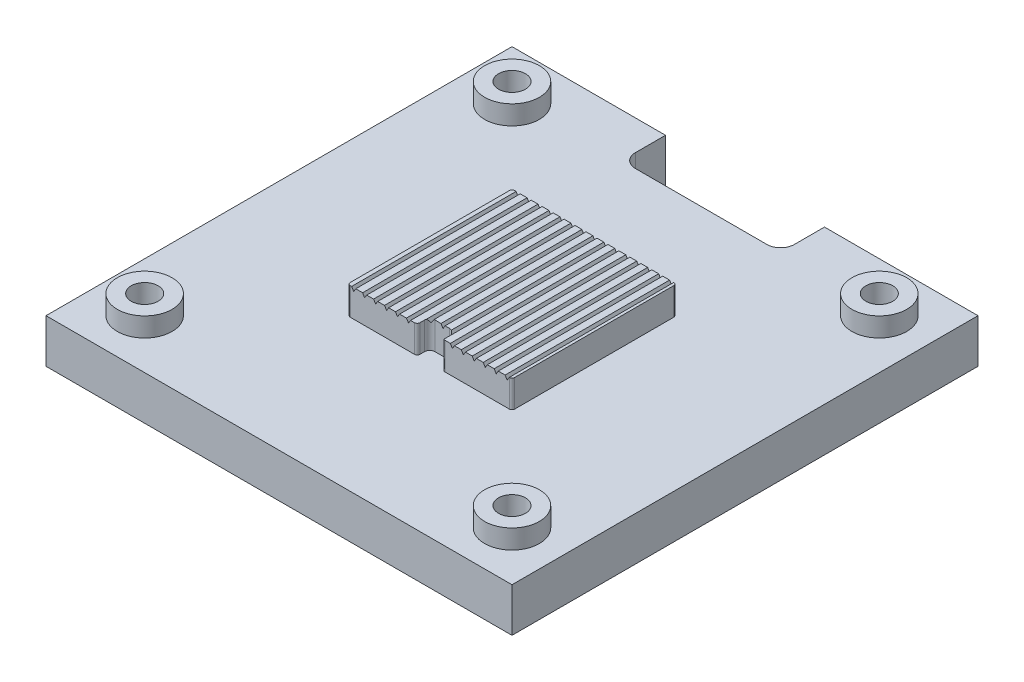
SolidWorks part; units mm, degrees
ref_plane "Front Plane" through (0, 0, 0) normal (0, 0, 1) x (1, 0, 0)
ref_plane "Top Plane" through (0, 0, 0) normal (0, 1, 0) x (1, 0, 0)
ref_plane "Right Plane" through (0, 0, 0) normal (1, 0, 0) x (0, 0, -1)
sketch "Sketch1" plane through (0, 0, 0) normal (0, 1, 0) x (1, 0, 0)
  line L0 (-71.3469, 0) -> (71.3469, 0) construction
  line L1 (-42.5, 42.5) -> (42.5, 42.5)
  line L2 (-42.5, 42.5) -> (-42.5, -42.5)
  line L3 (-42.5, -42.5) -> (42.5, -42.5)
  line L4 (42.5, 42.5) -> (42.5, -42.5)
  line L5 (-42.5, 42.5) -> (42.5, -42.5) construction
  line L6 (-42.5, -42.5) -> (42.5, 42.5) construction
  line L7 (0, -59.0713) -> (0, 59.0713) construction
  circle A0 centre (-33.5, 33.5) radius 2.4575
  circle A1 centre (-33.5, -33.5) radius 2.4575
  circle A2 centre (33.5, -33.5) radius 2.4575
  circle A3 centre (33.5, 33.5) radius 2.4575
  point P0 (0, 0)
  dimension "D3" = 4.915
  dimension "D1" = 85
  dimension "D2" = 85
  dimension "D4" = 9
  dimension "D5" = 9
extrude "Boss-Extrude1" add sketch "Sketch1" along normal blind 8
sketch "Sketch2" plane through (0, 0, 0) normal (0, -1, 0) x (1, 0, 0)
  line L0 (0, -4.4) -> (0, 4.4) construction
  line L1 (4.4, 0) -> (-4.4, 0) construction
  circle A0 centre (-33.5, 33.5) radius 3.969
  circle A1 centre (33.5, 33.5) radius 3.969
  circle A2 centre (33.5, -33.5) radius 3.969
  circle A3 centre (-33.5, -33.5) radius 3.969
  dimension "D1" = 7.938
extrude "Cut-Extrude1" cut sketch "Sketch2" against normal blind 4.166
sketch "Sketch3" plane through (0, 8, 0) normal (0, 1, 0) x (1, 0, 0)
  line L0 (0, -4.4) -> (0, 4.4) construction
  line L1 (-4.4, 0) -> (4.4, 0) construction
  circle A0 centre (33.5, -33.5) radius 5
  circle A1 centre (33.5, -33.5) radius 2.4575
  circle A2 centre (33.5, -33.5) radius 2.4575 construction
  circle A3 centre (-33.5, -33.5) radius 2.4575
  circle A4 centre (-33.5, -33.5) radius 5
  circle A5 centre (-33.5, 33.5) radius 5
  circle A6 centre (-33.5, 33.5) radius 2.4575
  circle A7 centre (33.5, 33.5) radius 2.4575
  circle A8 centre (33.5, 33.5) radius 5
  dimension "D1" = 10
extrude "Boss-Extrude2" add sketch "Sketch3" along normal blind 3.5
sketch "Sketch4" plane through (0, 8, 0) normal (0, 1, 0) x (1, 0, 0)
  line L0 (2.2929, -14.5) -> (2.2929, -13.7071)
  line L1 (14.5, -15) -> (2.7929, -15)
  line L2 (15, -14.5) -> (15, 14.5)
  line L3 (14.5, 15) -> (-14.5, 15)
  line L4 (-15, -14.5) -> (-15, 14.5)
  line L5 (15, -15) -> (-15, 15) construction
  line L6 (15, 15) -> (-15, -15) construction
  line L7 (1.2929, -12.7071) -> (-1.2929, -12.7071)
  line L8 (-2.2929, -13.7071) -> (-2.2929, -14.5)
  line L9 (-2.7929, -15) -> (-14.5, -15)
  arc A0 (-14.5, 15) -> (-15, 14.5) centre (-14.5, 14.5) ccw
  arc A1 (15, 14.5) -> (14.5, 15) centre (14.5, 14.5) ccw
  arc A2 (-14.5, -15) -> (-15, -14.5) centre (-14.5, -14.5) cw
  arc A3 (14.5, -15) -> (15, -14.5) centre (14.5, -14.5) ccw
  arc A4 (-2.2929, -14.5) -> (-2.7929, -15) centre (-2.7929, -14.5) cw
  arc A5 (2.2929, -14.5) -> (2.7929, -15) centre (2.7929, -14.5) ccw
  arc A6 (-1.2929, -12.7071) -> (-2.2929, -13.7071) centre (-1.2929, -13.7071) ccw
  arc A7 (2.2929, -13.7071) -> (1.2929, -12.7071) centre (1.2929, -13.7071) ccw
  point P0 (0, 0)
  point P10 (0, -12.7071)
  point P25 (-2.2929, -15)
  point P30 (-2.2929, -12.7071)
  point P33 (2.2929, -12.7071)
  dimension "D4" = 0.5
  dimension "D6" = 0.5
  dimension "D7" = 1
  dimension "D1" = 30
  dimension "D2" = 2.2929
  dimension "D3" = 4.5858
  dimension "D5" = 30
extrude "Boss-Extrude3" add sketch "Sketch4" along normal blind 5
sketch "Sketch5" plane through (0, 8, 0) normal (0, 1, 0) x (1, 0, 0)
  line L0 (42.5, 42.5) -> (-42.5, 42.5) construction
  line L1 (14.5, 42.5) -> (-14.5, 42.5)
  line L2 (14.5, 42.5) -> (14.5, 34.5)
  line L3 (14.5, 34.5) -> (-14.5, 34.5)
  line L4 (-14.5, 42.5) -> (-14.5, 34.5)
  point P6 (0, 34.5)
  dimension "D1" = 29
  dimension "D2" = 8
extrude "Cut-Extrude2" cut sketch "Sketch5" against normal blind 10
fillet "Fillet1" radius 2.5 2 edges at (-14.5, 4, -34.5) (14.5, 4, -34.5)
sketch "Sketch7" plane through (0, 0, -15) normal (0, 0, -1) x (-1, 0, 0)
  line L0 (-14.5, 13) -> (-14.125, 12.38)
  line L1 (-14.125, 12.38) -> (-13.75, 13)
  line L2 (-14.5, 13) -> (14.5, 13) construction
  line L3 (-13.75, 13) -> (-14.5, 13)
  line L4 (-12.5, 13) -> (-12.125, 12.38)
  line L5 (-12.125, 12.38) -> (-11.75, 13)
  line L6 (-11.75, 13) -> (-12.5, 13)
  line L7 (-10.5, 13) -> (-10.125, 12.38)
  line L8 (-10.125, 12.38) -> (-9.75, 13)
  line L9 (-9.75, 13) -> (-10.5, 13)
  line L10 (-8.5, 13) -> (-8.125, 12.38)
  line L11 (-8.125, 12.38) -> (-7.75, 13)
  line L12 (-7.75, 13) -> (-8.5, 13)
  line L13 (-6.5, 13) -> (-6.125, 12.38)
  line L14 (-6.125, 12.38) -> (-5.75, 13)
  line L15 (-5.75, 13) -> (-6.5, 13)
  line L16 (-4.5, 13) -> (-4.125, 12.38)
  line L17 (-4.125, 12.38) -> (-3.75, 13)
  line L18 (-3.75, 13) -> (-4.5, 13)
  line L19 (-2.5, 13) -> (-2.125, 12.38)
  line L20 (-2.125, 12.38) -> (-1.75, 13)
  line L21 (-1.75, 13) -> (-2.5, 13)
  line L22 (-0.5, 13) -> (-0.125, 12.38)
  line L23 (-0.125, 12.38) -> (0.25, 13)
  line L24 (0.25, 13) -> (-0.5, 13)
  line L25 (1.5, 13) -> (1.875, 12.38)
  line L26 (1.875, 12.38) -> (2.25, 13)
  line L27 (2.25, 13) -> (1.5, 13)
  line L28 (3.5, 13) -> (3.875, 12.38)
  line L29 (3.875, 12.38) -> (4.25, 13)
  line L30 (4.25, 13) -> (3.5, 13)
  line L31 (5.5, 13) -> (5.875, 12.38)
  line L32 (5.875, 12.38) -> (6.25, 13)
  line L33 (6.25, 13) -> (5.5, 13)
  line L34 (7.5, 13) -> (7.875, 12.38)
  line L35 (7.875, 12.38) -> (8.25, 13)
  line L36 (8.25, 13) -> (7.5, 13)
  line L37 (9.5, 13) -> (9.875, 12.38)
  line L38 (9.875, 12.38) -> (10.25, 13)
  line L39 (10.25, 13) -> (9.5, 13)
  line L40 (11.5, 13) -> (11.875, 12.38)
  line L41 (11.875, 12.38) -> (12.25, 13)
  line L42 (12.25, 13) -> (11.5, 13)
  line L43 (13.5, 13) -> (13.875, 12.38)
  line L44 (13.875, 12.38) -> (14.25, 13)
  line L45 (14.25, 13) -> (13.5, 13)
  dimension "D1" = 0.375
  dimension "D2" = 0.375
  dimension "D3" = 0.62
  dimension "D4" = 15
extrude "Cut-Extrude3" cut sketch "Sketch7" against normal up to next
